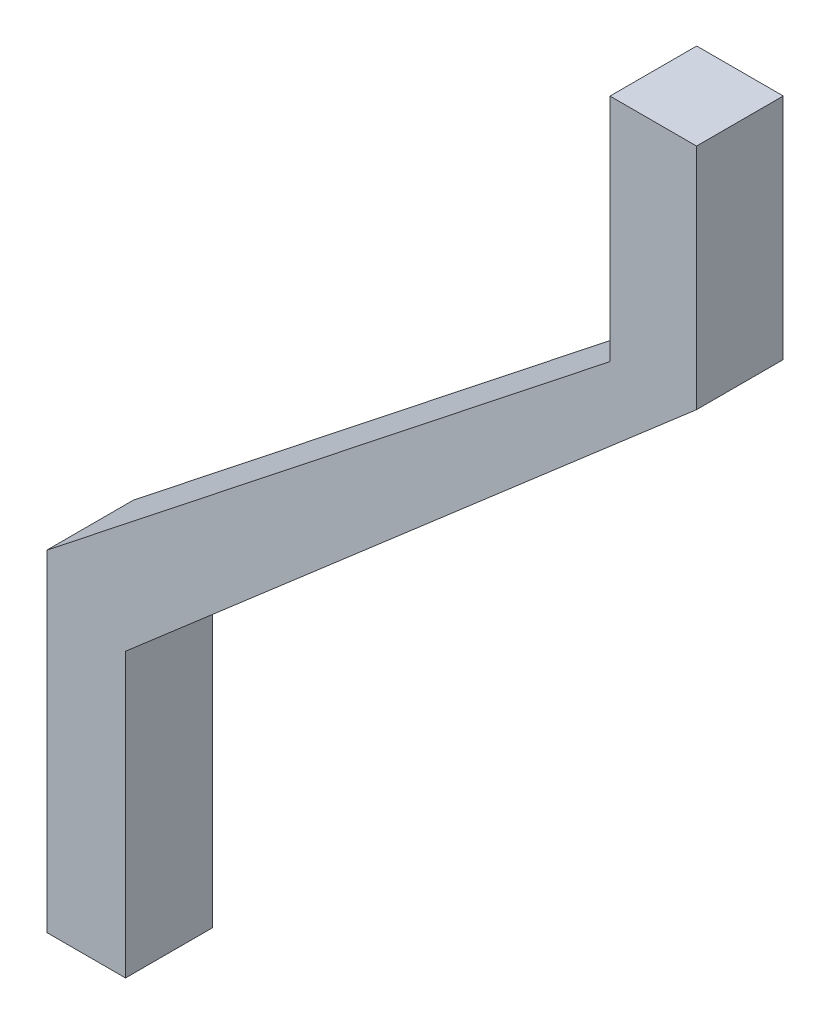
SolidWorks part; units mm, degrees
ref_plane "Front Plane" through (0, 0, 0) normal (0, 0, 1) x (1, 0, 0)
ref_plane "Top Plane" through (0, 0, 0) normal (0, 1, 0) x (1, 0, 0)
ref_plane "Right Plane" through (0, 0, 0) normal (1, 0, 0) x (0, 0, -1)
sketch "Sketch1" plane through (0, 0, 0) normal (0, 0, 1) x (1, 0, 0)
  line L0 (0, 0) -> (0, -26.5206)
  line L1 (0, -26.5206) -> (-64.9462, -77.8186)
  line L2 (-64.9462, -77.8186) -> (-64.9462, -116.0033)
  line L3 (-64.9462, -116.0033) -> (-55.8619, -116.0033)
  line L4 (-55.8619, -116.0033) -> (-55.8619, -83.3718)
  line L5 (-55.8619, -83.3718) -> (9.9806, -26.3292)
  line L6 (9.9806, -26.3292) -> (9.9806, 0)
  line L7 (0, 0) -> (9.9806, 0)
extrude "Boss-Extrude1" add sketch "Sketch1" along normal blind 10
